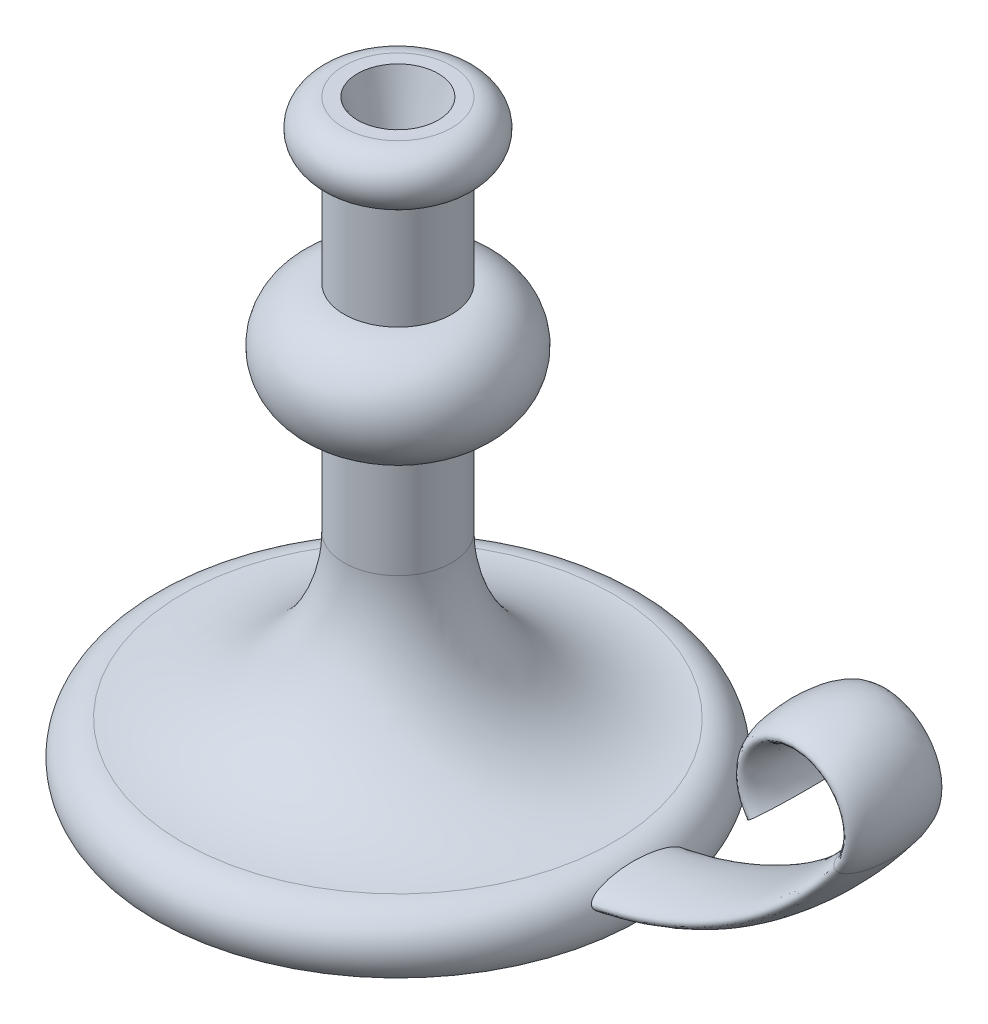
SolidWorks part; units mm, degrees
ref_plane "Płaszczyzna przednia" through (0, 0, 0) normal (0, 0, 1) x (1, 0, 0)
ref_plane "Płaszczyzna górna" through (0, 0, 0) normal (0, 1, 0) x (1, 0, 0)
ref_plane "Płaszczyzna prawa" through (0, 0, 0) normal (1, 0, 0) x (0, 0, -1)
sketch "Szkic1" plane through (0, 0, 0) normal (0, 0, 1) x (1, 0, 0)
  line L0 (0, 0) -> (0, 220)
  line L1 (0, 220) -> (20, 220)
  line L2 (20, 200) -> (20, 160)
  line L3 (20, 120) -> (20, 80)
  line L4 (90, 0) -> (0, 0)
  arc A0 (20, 220) -> (20, 200) centre (20, 210) cw
  arc A1 (20, 160) -> (20, 120) centre (20, 140) cw
  arc A2 (20, 80) -> (80, 20) centre (80, 80) ccw
  arc A3 (80, 20) -> (90, 0) centre (80, 7.5) cw
  dimension "D3" = 10
  dimension "D5" = 20
  dimension "D6" = 60
  dimension "D7" = 12.5
  dimension "D1" = 220
  dimension "D2" = 20
  dimension "D4" = 40
  dimension "D8" = 90
  dimension "D9" = 80
revolve "Obrót1" add sketch "Szkic1" angle 360 about L0
sketch "Szkic2" plane through (0, 0, 0) normal (0, 0, 1) x (1, 0, 0)
  line L0 (0, 10) -> (60, 10)
  line L1 (-90, 0) -> (90, 0) construction
  arc A0 (60, 10) -> (180, 70) centre (60, 160) ccw
  arc A1 (180, 70) -> (148, 70) centre (164, 82) ccw
  dimension "D3" = 150
  dimension "D4" = 20
  dimension "D1" = 60
  dimension "D2" = 10
  dimension "D5" = 60
sketch "Szkic3" plane through (0, 0, 0) normal (1, 0, 0) x (0, 0, -1)
  line L0 (0, 70) -> (0, 10) construction
  line L1 (-90, 0) -> (90, 0) construction
  ellipse E0 centre (0, 10) end of major axis (17.5, 10) minor radius 5
  point P10 (0, 0)
  dimension "D1" = 17.5
  dimension "D2" = 10
  dimension "D3" = 5
  dimension "D4" = 10
sweep "Wyciągnięcie po ścieżce1" add profiles "Szkic3" path "Szkic2"
sketch "Szkic4" plane through (0, 220, 0) normal (0, 1, 0) x (1, 0, 0)
  circle A0 centre (0, 0) radius 15
  dimension "D1" = 30
extrude "Wytnij-wyciągnięcie1" cut sketch "Szkic4" against normal blind 25 draft 15
